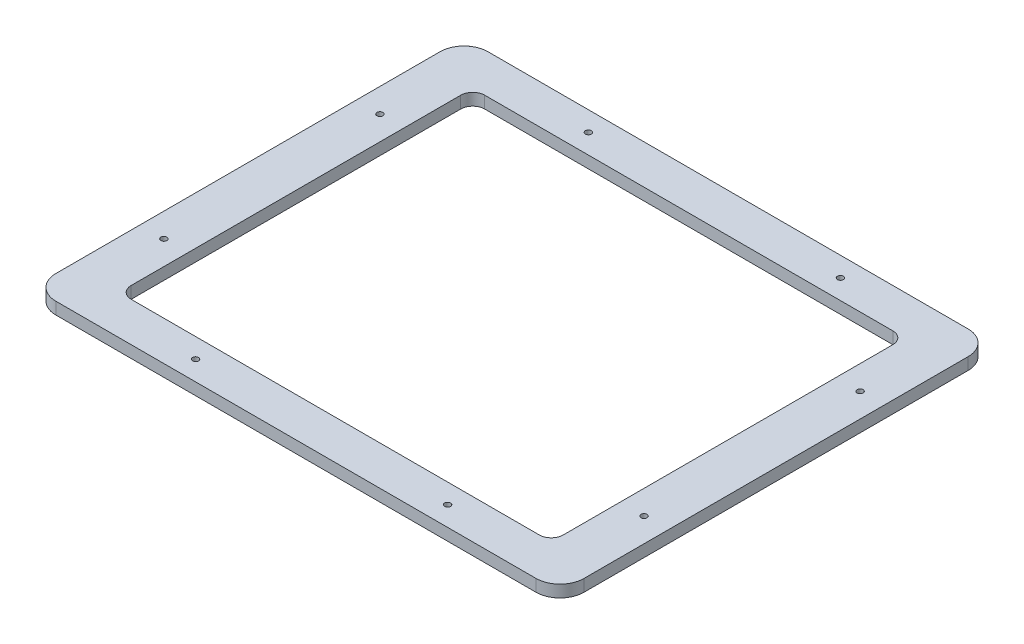
SolidWorks part; units mm, degrees
ref_plane "Front Plane" through (0, 0, 0) normal (0, 0, 1) x (1, 0, 0)
ref_plane "Top Plane" through (0, 0, 0) normal (0, 1, 0) x (1, 0, 0)
ref_plane "Right Plane" through (0, 0, 0) normal (1, 0, 0) x (0, 0, -1)
sketch "Sketch1" plane through (0, 0, 0) normal (0, 1, 0) x (1, 0, 0)
  line L1 (-139.7, 114.3) -> (139.7, 114.3)
  line L2 (-139.7, 114.3) -> (-139.7, -114.3)
  line L3 (-139.7, -114.3) -> (139.7, -114.3)
  line L4 (139.7, 114.3) -> (139.7, -114.3)
  line L5 (-139.7, 114.3) -> (139.7, -114.3) construction
  line L6 (-139.7, -114.3) -> (139.7, 114.3) construction
  line L7 (-114.3, 93.5182) -> (114.3, 93.5182)
  line L8 (-114.3, 93.5182) -> (-114.3, -93.5182)
  line L9 (-114.3, -93.5182) -> (114.3, -93.5182)
  line L10 (114.3, 93.5182) -> (114.3, -93.5182)
  line L11 (-114.3, 93.5182) -> (114.3, -93.5182) construction
  line L12 (-114.3, -93.5182) -> (114.3, 93.5182) construction
  point P0 (0, 0)
  point P6 (0, 0)
  dimension "D1" = 279.4
  dimension "D2" = 228.6
  dimension "D3" = 25.4
extrude "Boss-Extrude1" add sketch "Sketch1" along normal blind 6.35
sketch "Sketch2" plane through (0, 6.35, 0) normal (0, 1, 0) x (1, 0, 0)
  line L0 (0, 114.3) -> (0, 93.5182) construction
  line L1 (139.7, 114.3) -> (-139.7, 114.3) construction
  line L2 (114.3, 93.5182) -> (-114.3, 93.5182) construction
  line L3 (-139.7, 103.9091) -> (139.7, 103.9091) construction
  line L4 (-139.7, 114.3) -> (-139.7, -114.3) construction
  line L5 (139.7, -114.3) -> (139.7, 114.3) construction
  line L6 (0, 0) -> (236.5749, 0) construction
  line L7 (-139.7, 0) -> (-114.3, 0) construction
  line L8 (-114.3, 93.5182) -> (-114.3, -93.5182) construction
  line L9 (-114.3, 0) -> (-127, 0) construction
  line L10 (-127, 0) -> (-127, 114.3) construction
  line L11 (114.3, 0) -> (139.7, 0) construction
  line L12 (114.3, -93.5182) -> (114.3, 93.5182) construction
  line L13 (127, 0) -> (127, 114.3) construction
  circle A0 centre (-63.5, 103.9091) radius 1.5875
  circle A1 centre (-63.5, -103.9091) radius 1.5875
  circle A2 centre (69.85, 103.9091) radius 1.5875
  circle A3 centre (69.85, -103.9091) radius 1.5875
  circle A4 centre (-127, 57.15) radius 1.5875
  circle A5 centre (-127, -57.15) radius 1.5875
  circle A6 centre (127, 57.15) radius 1.5875
  circle A7 centre (127, -57.15) radius 1.5875
  point P12 (0, 103.9091)
  dimension "D1" = 3.175
  dimension "D3" = 69.85
  dimension "D2" = 76.2
  dimension "D4" = 57.15
extrude "Cut-Extrude1" cut sketch "Sketch2" against normal through all
fillet "Fillet1" radius 12.7 4 edges at (-139.7, 3.175, 114.3) (139.7, 3.175, 114.3) (139.7, 3.175, -114.3) (-139.7, 3.175, -114.3)
fillet "Fillet2" radius 6.35 4 edges at (-114.3, 3.175, 93.5182) (114.3, 3.175, 93.5182) (114.3, 3.175, -93.5182) (-114.3, 3.175, -93.5182)
